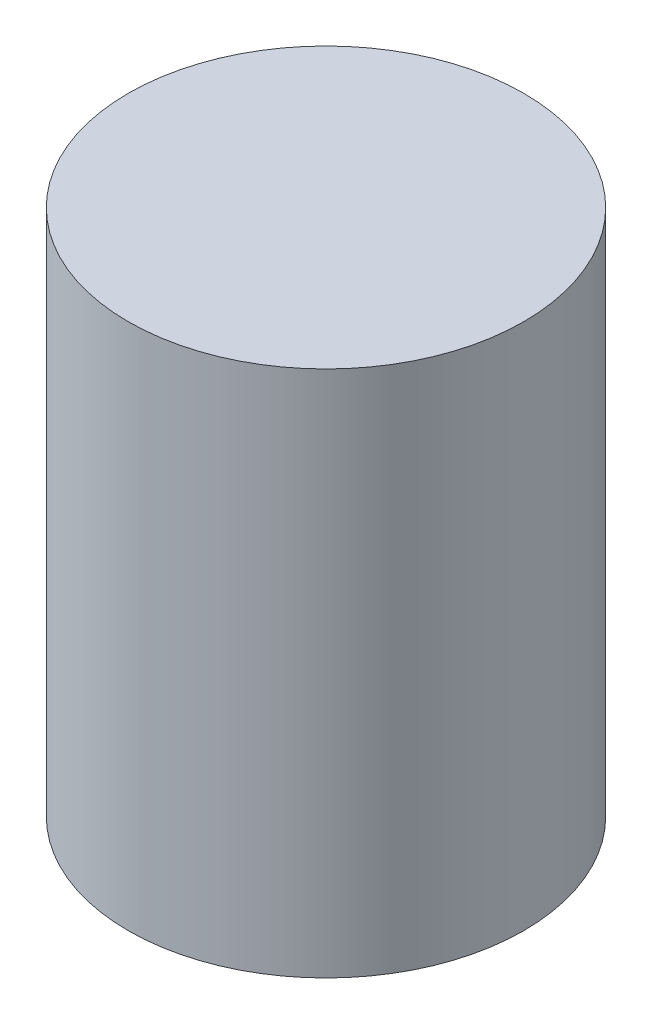
SolidWorks part; units mm, degrees
ref_plane "Front Plane" through (0, 0, 0) normal (0, 0, 1) x (1, 0, 0)
ref_plane "Top Plane" through (0, 0, 0) normal (0, 1, 0) x (1, 0, 0)
ref_plane "Right Plane" through (0, 0, 0) normal (1, 0, 0) x (0, 0, -1)
sketch "Sketch1" plane through (0, 0, 0) normal (0, 1, 0) x (1, 0, 0)
  circle A0 centre (0, 0) radius 7.5
  dimension "D1" = 15
extrude "Boss-Extrude1" add sketch "Sketch1" along normal blind 20
